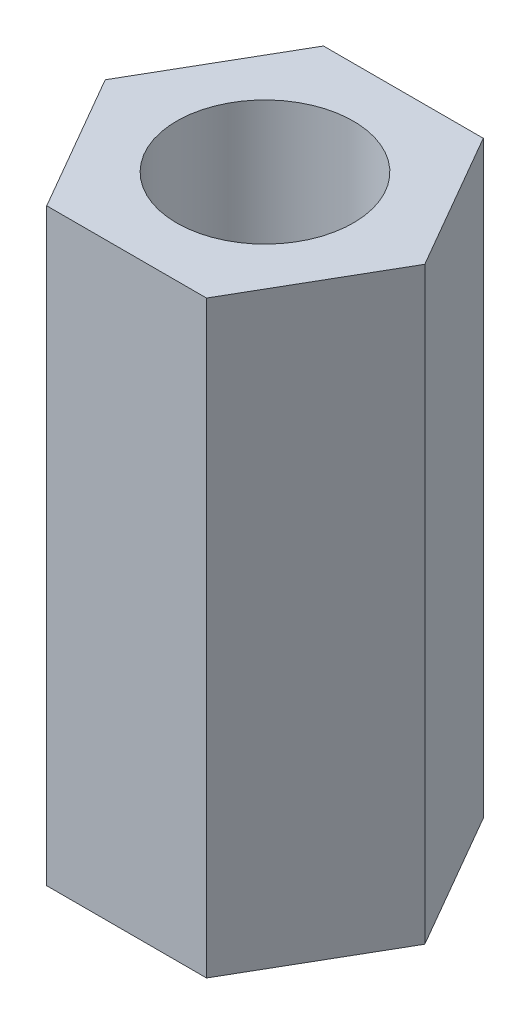
SolidWorks part; units mm, degrees
material "黄铜"
ref_plane "前视基准面" through (0, 0, 0) normal (0, 0, 1) x (1, 0, 0)
ref_plane "上视基准面" through (0, 0, 0) normal (0, 1, 0) x (1, 0, 0)
ref_plane "右视基准面" through (0, 0, 0) normal (1, 0, 0) x (0, 0, -1)
sketch "草图1" plane through (0, 0, 0) normal (0, 1, 0) x (1, 0, 0)
  line L1 (2.7135, 0) -> (1.3568, 2.35)
  line L2 (1.3568, 2.35) -> (-1.3568, 2.35)
  line L3 (-1.3568, 2.35) -> (-2.7135, 0)
  line L4 (-2.7135, 0) -> (-1.3568, -2.35)
  line L5 (-1.3568, -2.35) -> (1.3568, -2.35)
  line L6 (1.3568, -2.35) -> (2.7135, 0)
  circle A0 centre (0, 0) radius 2.35 construction
  circle A1 centre (0, 0) radius 1.5
  dimension "D2" = 3
  dimension "D1" = 4.7
extrude "凸台-拉伸1" add sketch "草图1" along normal blind 10
